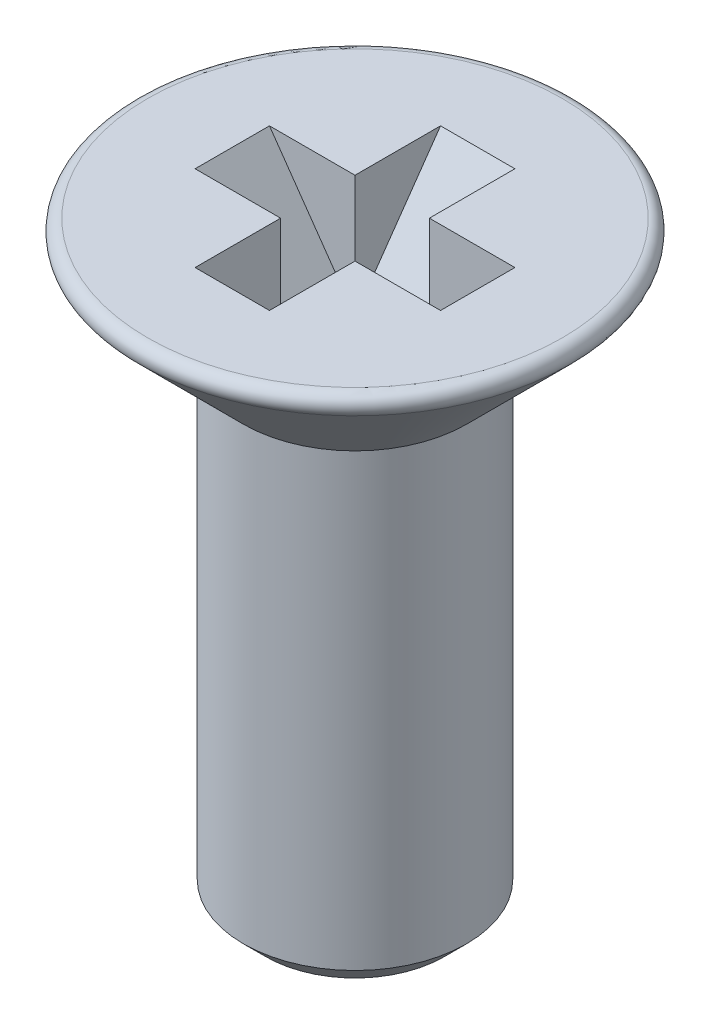
SolidWorks part; units mm, degrees
ref_plane "Plan de face" through (0, 0, 0) normal (0, 0, 1) x (1, 0, 0)
ref_plane "Plan de dessus" through (0, 0, 0) normal (0, 1, 0) x (1, 0, 0)
ref_plane "Plan de droite" through (0, 0, 0) normal (1, 0, 0) x (0, 0, -1)
sketch "Esquisse1" plane through (0, 0, 0) normal (0, 0, 1) x (1, 0, 0)
  line L0 (0, 0) -> (-2.7879, 0)
  line L1 (-2.8939, -0.2561) -> (-1.5, -1.65)
  line L2 (-1.5, -1.65) -> (-1.5, -7.7)
  line L3 (-1.2, -8) -> (0, -8)
  line L4 (0, -8) -> (0, 0) construction
  line L5 (-1.5, -7.7) -> (-1.2, -8)
  line L6 (0, 0) -> (0, -8)
  arc A0 (-2.8939, -0.2561) -> (-2.7879, 0) centre (-2.7879, -0.15) cw
  point P2 (-1.5, -8)
  point P8 (-3.15, 0)
  point P9 (-3.15, 0)
  dimension "D2" = 0.15
  dimension "D3" = 0.3
  dimension "D1" = 45
  dimension "D4" = 0.3
revolve "Révolution1" add sketch "Esquisse1" angle 360 about L4
sketch "Esquisse4" plane through (0, 0, 0) normal (0, 0, 1) x (1, 0, 0)
  line L0 (-1.65, 0) -> (1.65, 0)
  line L1 (2.7879, 0) -> (-2.7879, 0) construction
  line L2 (1.65, 0) -> (0.5444, -1.5789)
  line L3 (0.5444, -1.5789) -> (-0.5444, -1.5789)
  line L4 (0, -8) -> (0, 0) construction
  line L5 (0, -1.5789) -> (0, 0) construction
  line L6 (-1.65, 0) -> (-0.5444, -1.5789)
  dimension "D1" = 3.3
  dimension "D2" = 1.5789
  dimension "D3" = 55
extrude "Enlèv. mat.-Extru.2" cut sketch "Esquisse4" against normal mid plane 1
pattern_circular "Répétition circulaire2" count 2 every 90 about axis through (0, 0, 0) along (0, 1, 0) of "Enlèv. mat.-Extru.2"
equation "\"D2@Esquisse1\" = \"D\"/20"
equation "\"D3@Esquisse1\" = \"D\"/10"
equation "\"D4@Esquisse1\" = \"D\"/10"
equation "\"D1@Esquisse4\" = \"D\"*1.1"
equation "\"D2@Esquisse4\" = \"D\"/1.9"
